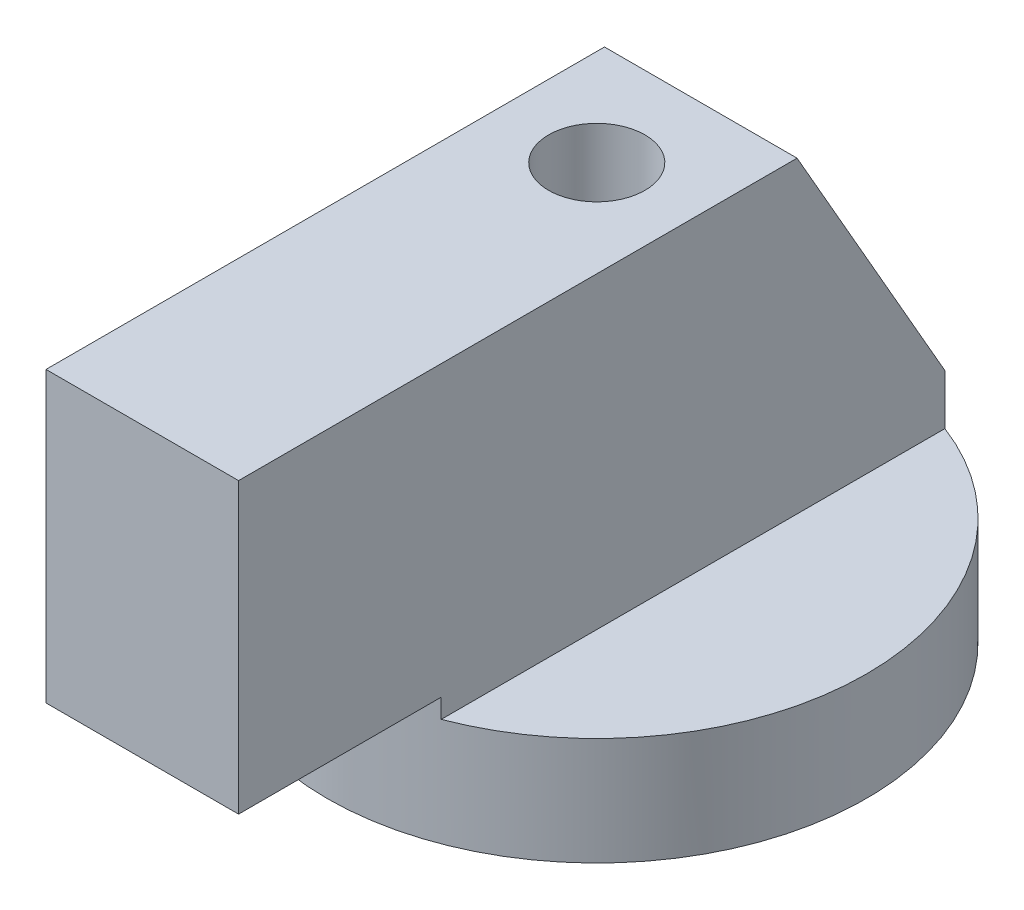
SolidWorks part; units mm, degrees
ref_plane "Ön Düzlem" through (0, 0, 0) normal (0, 0, 1) x (1, 0, 0)
ref_plane "Üst Düzlem" through (0, 0, 0) normal (0, 1, 0) x (1, 0, 0)
ref_plane "Sağ Düzlem" through (0, 0, 0) normal (1, 0, 0) x (0, 0, -1)
sketch "Çizim1" plane through (0, 0, 0) normal (0, 1, 0) x (1, 0, 0)
  circle A0 centre (0, 0) radius 14
  dimension "D1" = 28
extrude "Yükseklik-Ekstrüzyon1" add sketch "Çizim1" against normal blind 5.6
sketch "Çizim2" plane through (0, 0, 0) normal (1, 0, 0) x (0, 0, -1)
  line L0 (-14, 0) -> (-14, 1)
  line L1 (-14, 1) -> (-23.6, 1)
  line L2 (-23.6, 1) -> (-23.6, 16)
  line L3 (-23.6, 16) -> (5.4, 16)
  line L4 (5.4, 16) -> (14, 1)
  line L5 (14, 1) -> (14, 0)
  line L6 (14, 0) -> (-14, 0)
  line L7 (-14, -5.6) -> (14, -5.6) construction
  line L8 (14, -5.6) -> (14, 0) construction
  dimension "D1" = 15
  dimension "D2" = 21.6
  dimension "D3" = 29
  dimension "D4" = 37.6
extrude "Yükseklik-Ekstrüzyon2" add sketch "Çizim2" along normal mid plane 10
sketch "Çizim3" plane through (0, -5.6, 0) normal (0, -1, 0) x (1, 0, 0)
  circle A0 centre (0, 0) radius 14
extrude "Kes-Ekstrüzyon1" cut sketch "Çizim3" against normal up to surface (6.6 mm away) flip side to cut up to face at (0, 1, 18.8)
sketch "Çizim4" plane through (0, -5.6, 0) normal (0, -1, 0) x (1, 0, 0)
  line L1 (-5, -14) -> (5, -14)
  line L2 (-5, -14) -> (-5, -13.0767)
  line L4 (5, -14) -> (5, -13.0767)
  arc A0 (-5, -13.0767) -> (5, -13.0767) centre (0, 0) ccw
  circle M1 centre (0, 0) radius 14
extrude "Kes-Ekstrüzyon2" cut sketch "Çizim4" against normal blind 10 contours L1 L4 M1 | L2 L1 M1
sketch "Çizim5" plane through (0, -5.6, 0) normal (0, -1, 0) x (1, 0, 0)
  circle A0 centre (0, 0) radius 2.5
  dimension "D1" = 5
extrude "Kes-Ekstrüzyon3" cut sketch "Çizim5" against normal through all
sketch "Çizim6" plane through (0, 6.2883, -10.968) normal (0, 0.4974, -0.8675) x (-1, 0, 0)
  line L0 (-5, -4.2395) -> (-5, 11.1946) construction
  line L1 (1.75, 5.9326) -> (-1.75, 5.9326)
  line L2 (1.75, 5.9326) -> (1.75, -2.0674)
  line L3 (1.75, -2.0674) -> (-1.75, -2.0674)
  line L4 (-1.75, 5.9326) -> (-1.75, -2.0674)
  line L5 (1.75, 5.9326) -> (-1.75, -2.0674) construction
  line L6 (1.75, -2.0674) -> (-1.75, 5.9326) construction
  point P0 (0, 1.9326)
  dimension "D1" = 3.5
  dimension "D2" = 8
  dimension "D3" = 3.25
extrude "Yükseklik-Ekstrüzyon3" add sketch "Çizim6" along normal blind 0.1
